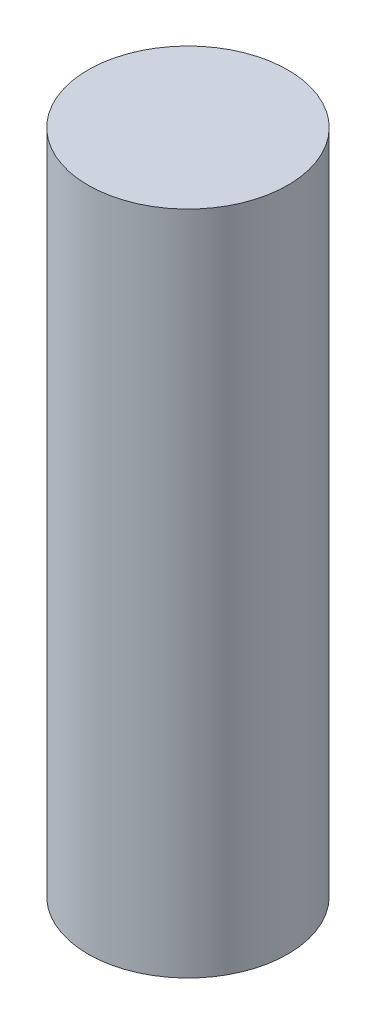
SolidWorks part; units mm, degrees
ref_plane "Front Plane" through (0, 0, 0) normal (0, 0, 1) x (1, 0, 0)
ref_plane "Top Plane" through (0, 0, 0) normal (0, 1, 0) x (1, 0, 0)
ref_plane "Right Plane" through (0, 0, 0) normal (1, 0, 0) x (0, 0, -1)
sketch "Sketch1" plane through (0, 0, 0) normal (0, 1, 0) x (1, 0, 0)
  circle A0 centre (0, 0) radius 6
  dimension "D1" = 12
extrude "Boss-Extrude1" add sketch "Sketch1" along normal blind 40
sketch "Sketch2" plane through (0, 0, 0) normal (0, -1, 0) x (1, 0, 0)
  line L0 (0, -2.66) -> (0, 2.09) construction
  line L1 (-1.6454, 2.09) -> (1.6454, 2.09)
  circle A1 centre (0, 0) radius 2.66
  dimension "D1" = 5.32
  dimension "D2" = 4.75
extrude "Cut-Extrude3" cut sketch "Sketch2" against normal blind 30 and the other way through all
